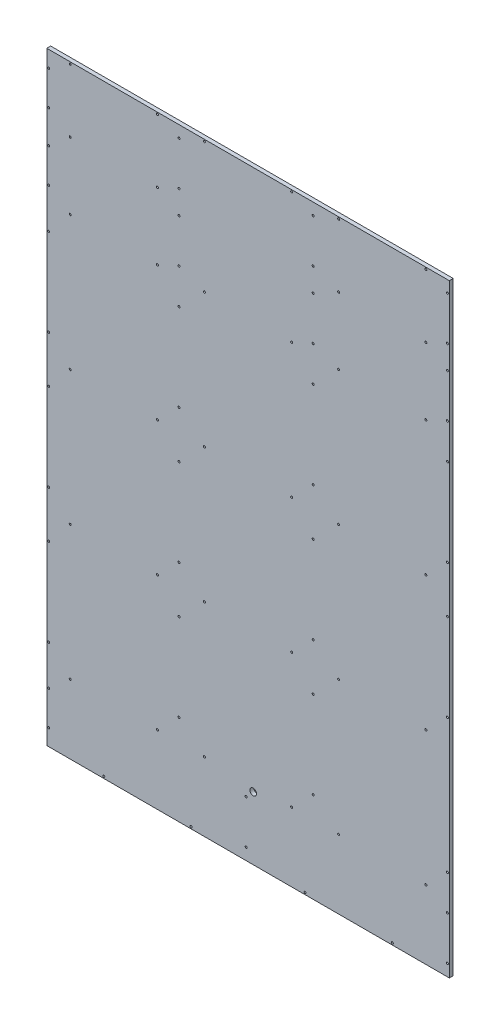
SolidWorks part; units mm, degrees
material "Acrylic (Medium-high impact)"
ref_plane "Front Plane" through (0, 0, 0) normal (0, 0, 1) x (1, 0, 0)
ref_plane "Top Plane" through (0, 0, 0) normal (0, 1, 0) x (1, 0, 0)
ref_plane "Right Plane" through (0, 0, 0) normal (1, 0, 0) x (0, 0, -1)
sketch "Sketch1" plane through (0, 0, 0) normal (0, 0, 1) x (1, 0, 0)
  line L0 (300, 0) -> (300, 100) construction
  line L1 (0, 0) -> (600, 0)
  line L2 (0, 0) -> (0, 900)
  line L3 (0, 900) -> (600, 900)
  line L4 (600, 0) -> (600, 900)
  line L5 (0, 300) -> (200, 300) construction
  line L6 (0, 100) -> (300, 100) construction
  line L7 (0, 500) -> (600, 500) construction
  line L8 (200, 100) -> (200, 300) construction
  line L10 (150, 5.8) -> (150, 0) construction
  line L11 (156.7, 5.8) -> (156.7, 0) construction
  line L12 (100, 105.8) -> (100, 100) construction
  line L13 (0, 700) -> (200, 700) construction
  line L14 (106.7, 705.8) -> (106.7, 700) construction
  line L15 (594.2, 15.8) -> (594.2, 84.2)
  line L16 (200, 700) -> (200, 800) construction
  line L17 (329.2, 5.8) -> (584.2, 5.8)
  line L20 (0, 294.2) -> (200, 294.2) construction
  line L21 (200, 300) -> (200, 294.2) construction
  line L22 (319.2, 84.2) -> (319.2, 15.8)
  line L23 (0, 200) -> (194.2, 200) construction
  line L25 (200, 300) -> (200, 100) construction
  line L26 (200, 100) -> (194.2, 100) construction
  line L27 (194.2, 300) -> (194.2, 100) construction
  line L28 (100, 294.2) -> (100, 105.8) construction
  line L29 (194.2, 115.8) -> (194.2, 284.2)
  line L30 (29.2, 105.8) -> (184.2, 105.8)
  line L31 (19.2, 284.2) -> (19.2, 115.8)
  line L32 (184.2, 294.2) -> (29.2, 294.2)
  line L37 (584.2, 94.2) -> (329.2, 94.2)
  line L43 (600, 0) -> (600, 100) construction
  line L44 (300, 100) -> (600, 100) construction
  line L46 (450, 5.8) -> (450, 0) construction
  line L47 (456.7, 5.8) -> (456.7, 0) construction
  line L48 (394.2, 115.8) -> (394.2, 284.2)
  line L55 (500, 100) -> (494.2, 100) construction
  line L57 (200, 800) -> (0, 800) construction
  line L58 (300, 100) -> (600, 100) construction
  line L59 (600, 100) -> (600, 0) construction
  line L60 (450, 100) -> (450, 5.8) construction
  line L61 (456.7, 94.2) -> (456.7, 100) construction
  line L62 (594.2, 50) -> (600, 50) construction
  line L63 (300, 50) -> (600, 50) construction
  line L64 (600, 100) -> (600, 0) construction
  line L69 (229.2, 105.8) -> (384.2, 105.8)
  line L70 (219.2, 284.2) -> (219.2, 115.8)
  line L71 (384.2, 294.2) -> (229.2, 294.2)
  line L72 (200, 300) -> (400, 300) construction
  line L74 (400, 100) -> (400, 300) construction
  line L75 (300, 105.8) -> (300, 100) construction
  line L76 (200, 294.2) -> (400, 294.2) construction
  line L78 (400, 300) -> (400, 294.2) construction
  line L79 (200, 200) -> (394.2, 200) construction
  line L80 (400, 300) -> (400, 100) construction
  line L85 (394.2, 300) -> (394.2, 100) construction
  line L86 (300, 294.2) -> (300, 105.8) construction
  line L87 (400, 300) -> (394.2, 300) construction
  line L88 (594.2, 115.8) -> (594.2, 284.2)
  line L89 (429.2, 105.8) -> (584.2, 105.8)
  line L90 (419.2, 284.2) -> (419.2, 115.8)
  line L91 (584.2, 294.2) -> (429.2, 294.2)
  line L92 (400, 300) -> (600, 300) construction
  line L93 (600, 100) -> (600, 300) construction
  line L94 (500, 105.8) -> (500, 100) construction
  line L95 (400, 294.2) -> (600, 294.2) construction
  line L96 (600, 300) -> (600, 294.2) construction
  line L101 (400, 200) -> (594.2, 200) construction
  line L102 (600, 300) -> (600, 100) construction
  line L103 (594.2, 300) -> (594.2, 100) construction
  line L104 (500, 294.2) -> (500, 105.8) construction
  line L105 (600, 300) -> (594.2, 300) construction
  line L106 (394.2, 315.8) -> (394.2, 484.2)
  line L107 (229.2, 305.8) -> (384.2, 305.8)
  line L108 (219.2, 484.2) -> (219.2, 315.8)
  line L109 (384.2, 494.2) -> (229.2, 494.2)
  line L110 (200, 500) -> (400, 500) construction
  line L111 (400, 300) -> (400, 500) construction
  line L112 (300, 305.8) -> (300, 300) construction
  line L117 (200, 494.2) -> (400, 494.2) construction
  line L118 (400, 500) -> (400, 494.2) construction
  line L119 (200, 400) -> (394.2, 400) construction
  line L120 (400, 500) -> (400, 300) construction
  line L121 (394.2, 500) -> (394.2, 300) construction
  line L122 (300, 494.2) -> (300, 305.8) construction
  line L123 (400, 500) -> (394.2, 500) construction
  line L124 (594.2, 315.8) -> (594.2, 484.2)
  line L125 (429.2, 305.8) -> (584.2, 305.8)
  line L126 (419.2, 484.2) -> (419.2, 315.8)
  line L127 (584.2, 494.2) -> (429.2, 494.2)
  line L128 (400, 500) -> (600, 500) construction
  line L133 (600, 300) -> (600, 500) construction
  line L134 (500, 305.8) -> (500, 300) construction
  line L135 (400, 494.2) -> (600, 494.2) construction
  line L136 (600, 500) -> (600, 494.2) construction
  line L137 (400, 400) -> (594.2, 400) construction
  line L138 (600, 500) -> (600, 300) construction
  line L139 (594.2, 500) -> (594.2, 300) construction
  line L142 (200, 300) -> (194.2, 300) construction
  line L144 (500, 494.2) -> (500, 305.8) construction
  line L149 (600, 500) -> (594.2, 500) construction
  line L150 (394.2, 515.8) -> (394.2, 684.2)
  line L151 (229.2, 505.8) -> (384.2, 505.8)
  line L152 (219.2, 684.2) -> (219.2, 515.8)
  line L153 (384.2, 694.2) -> (229.2, 694.2)
  line L154 (200, 700) -> (400, 700) construction
  line L155 (400, 500) -> (400, 700) construction
  line L156 (300, 505.8) -> (300, 500) construction
  line L157 (200, 694.2) -> (400, 694.2) construction
  line L158 (400, 700) -> (400, 694.2) construction
  line L159 (200, 600) -> (394.2, 600) construction
  line L160 (400, 700) -> (400, 500) construction
  line L165 (0, 100) -> (300, 100) construction
  line L166 (0, 100) -> (0, 0) construction
  line L171 (300, 100) -> (300, 0) construction
  line L176 (150, 100) -> (150, 5.8) construction
  line L177 (156.7, 94.2) -> (156.7, 100) construction
  line L178 (294.2, 50) -> (300, 50) construction
  line L179 (0, 50) -> (300, 50) construction
  line L180 (394.2, 700) -> (394.2, 500) construction
  line L181 (300, 100) -> (300, 0) construction
  line L182 (300, 0) -> (150, 0) construction
  line L183 (300, 694.2) -> (300, 505.8) construction
  line L184 (294.2, 15.8) -> (294.2, 84.2)
  line L185 (29.2, 5.8) -> (284.2, 5.8)
  line L186 (19.2, 84.2) -> (19.2, 15.8)
  line L187 (284.2, 94.2) -> (29.2, 94.2)
  line L188 (400, 700) -> (394.2, 700) construction
  line L189 (594.2, 515.8) -> (594.2, 684.2)
  line L192 (429.2, 505.8) -> (584.2, 505.8)
  line L193 (419.2, 684.2) -> (419.2, 515.8)
  line L194 (584.2, 694.2) -> (429.2, 694.2)
  line L197 (400, 700) -> (600, 700) construction
  line L203 (600, 500) -> (600, 700) construction
  line L204 (500, 505.8) -> (500, 500) construction
  line L206 (100, 700) -> (100, 800) construction
  line L207 (106.7, 794.2) -> (106.7, 800) construction
  line L208 (194.2, 750) -> (200, 750) construction
  line L209 (0, 750) -> (200, 750) construction
  line L211 (400, 694.2) -> (600, 694.2) construction
  line L212 (194.2, 715.8) -> (194.2, 784.2)
  line L213 (29.2, 705.8) -> (184.2, 705.8)
  line L214 (184.2, 794.2) -> (29.2, 794.2)
  line L215 (19.2, 784.2) -> (19.2, 715.8)
  line L220 (600, 700) -> (600, 694.2) construction
  line L222 (400, 600) -> (594.2, 600) construction
  line L223 (600, 700) -> (600, 500) construction
  line L225 (594.2, 700) -> (594.2, 500) construction
  line L226 (500, 694.2) -> (500, 505.8) construction
  line L228 (600, 700) -> (594.2, 700) construction
  line L230 (194.2, 315.8) -> (194.2, 484.2)
  line L235 (29.2, 305.8) -> (184.2, 305.8)
  line L236 (19.2, 484.2) -> (19.2, 315.8)
  line L237 (184.2, 494.2) -> (29.2, 494.2)
  line L238 (0, 500) -> (200, 500) construction
  line L239 (200, 300) -> (200, 500) construction
  line L240 (100, 305.8) -> (100, 300) construction
  line L241 (0, 494.2) -> (200, 494.2) construction
  line L242 (200, 500) -> (200, 494.2) construction
  line L243 (0, 400) -> (194.2, 400) construction
  line L244 (200, 500) -> (200, 300) construction
  line L245 (194.2, 500) -> (194.2, 300) construction
  line L246 (394.2, 833.4299) -> (394.2, 901.8299) [skipped]
  line L247 (229.2, 823.4299) -> (384.2, 823.4299) [skipped]
  line L248 (384.2, 911.8299) -> (229.2, 911.8299) [skipped]
  line L249 (219.2, 901.8299) -> (219.2, 833.4299) [skipped]
  line L250 (100, 494.2) -> (100, 305.8) construction
  line L251 (200, 500) -> (194.2, 500) construction
  line L252 (194.2, 515.8) -> (194.2, 684.2)
  line L253 (29.2, 505.8) -> (184.2, 505.8)
  line L254 (19.2, 684.2) -> (19.2, 515.8)
  line L255 (300, 817.6299) -> (300, 917.6299) construction
  line L256 (306.7, 911.8299) -> (306.7, 917.6299) construction
  line L257 (394.2, 867.6299) -> (400, 867.6299) construction
  line L258 (200, 867.6299) -> (400, 867.6299) construction
  line L259 (184.2, 694.2) -> (29.2, 694.2)
  line L260 (0, 700) -> (200, 700) construction
  line L265 (200, 500) -> (200, 700) construction
  line L266 (100, 505.8) -> (100, 500) construction
  line L267 (0, 694.2) -> (200, 694.2) construction
  line L268 (200, 700) -> (200, 694.2) construction
  line L269 (0, 600) -> (194.2, 600) construction
  line L270 (200, 700) -> (200, 500) construction
  line L271 (194.2, 700) -> (194.2, 500) construction
  line L272 (100, 694.2) -> (100, 505.8) construction
  line L273 (200, 700) -> (194.2, 700) construction
  line L274 (394.2, 715.8) -> (394.2, 784.2)
  line L275 (229.2, 705.8) -> (384.2, 705.8)
  line L280 (384.2, 794.2) -> (229.2, 794.2)
  line L281 (219.2, 784.2) -> (219.2, 715.8)
  line L282 (306.7, 705.8) -> (306.7, 700) construction
  line L283 (400, 700) -> (400, 800) construction
  line L285 (400, 800) -> (200, 800) construction
  line L286 (300, 700) -> (300, 800) construction
  line L288 (306.7, 794.2) -> (306.7, 800) construction
  line L290 (394.2, 750) -> (400, 750) construction
  line L291 (219.2, 783.65) -> (219.2, 750) [skipped]
  line L292 (394.2, 716.35) -> (394.2, 750) [skipped]
  line L293 (300, 705.8) -> (383.65, 705.8) [skipped]
  line L294 (200, 750) -> (300, 750) construction
  line L295 (300, 793.65) -> (300, 800) construction
  line L296 (306.7, 794.2) -> (306.7, 800) construction
  line L297 (306.15, 794.2) -> (300, 794.2) [skipped]
  line L298 (106.7, 911.8299) -> (106.7, 917.6299) construction
  line L299 (106.1501, 911.8299) -> (28.6501, 911.8299) [skipped]
  line L300 (0, 867.6299) -> (18.65, 867.6299) construction
  line L301 (19.2, 850) -> (19.2, 816.35) [skipped]
  line L302 (100, 823.4299) -> (183.65, 823.4299) [skipped]
  line L303 (100, 800) -> (100, 806.35) construction
  line L304 (194.2, 867.6299) -> (200, 867.6299) construction
  line L305 (194.2, 850) -> (194.2, 883.65) [skipped]
  line L306 (394.2, 750) -> (400, 750) construction
  line L307 (200, 750) -> (400, 750) construction
  line L308 (594.2, 715.8) -> (594.2, 784.2)
  line L309 (429.2, 705.8) -> (584.2, 705.8)
  line L310 (584.2, 794.2) -> (429.2, 794.2)
  line L311 (394.2, 115.8) -> (394.2, 284.2) [skipped]
  line L312 (229.2, 105.8) -> (384.2, 105.8) [skipped]
  line L313 (219.2, 284.2) -> (219.2, 115.8) [skipped]
  line L314 (384.2, 294.2) -> (229.2, 294.2) [skipped]
  line L315 (300, 294.2) -> (300, 105.8) construction
  line L316 (200, 200) -> (394.2, 200) construction
  line L317 (394.2, 315.8) -> (394.2, 484.2) [skipped]
  line L318 (219.2, 484.2) -> (219.2, 315.8) [skipped]
  line L319 (384.2, 494.2) -> (229.2, 494.2) [skipped]
  line L320 (200, 494.2) -> (400, 494.2) construction
  line L321 (419.2, 784.2) -> (419.2, 715.8)
  line L322 (200, 400) -> (394.2, 400) construction
  line L323 (394.2, 513.7835) -> (394.2, 300) construction
  line L324 (300, 494.2) -> (300, 305.8) construction
  line L325 (229.2, 305.8) -> (384.2, 305.8) [skipped]
  line L326 (506.7, 705.8) -> (506.7, 700) construction
  line L327 (400, 300) -> (394.2, 300) construction
  line L328 (394.2, 300) -> (394.2, 294.2) construction
  line L329 (400, 100) -> (394.2, 100) construction
  line L330 (400, 294.2) -> (400, 300) construction
  line L331 (600, 700) -> (600, 800) construction
  line L332 (201.4757, 294.2) -> (300.7378, 294.2) construction
  line L333 (400, 313.7835) -> (400, 293.1) construction
  line L334 (600, 800) -> (400, 800) construction
  line L335 (400, 300) -> (400, 294.2) construction
  line L336 (194.2, 315.8) -> (194.2, 484.2) [skipped]
  line L337 (29.2, 305.8) -> (184.2, 305.8) [skipped]
  line L338 (19.2, 484.2) -> (19.2, 315.8) [skipped]
  line L339 (184.2, 494.2) -> (29.2, 494.2) [skipped]
  line L340 (400, 494.2) -> (400, 500) construction
  line L341 (500, 700) -> (500, 800) construction
  line L342 (506.7, 794.2) -> (506.7, 800) construction
  line L343 (400, 513.7835) -> (400, 493.1) construction
  line L344 (594.2, 750) -> (600, 750) construction
  line L345 (400, 500) -> (400, 494.2) construction
  line L346 (200, 300) -> (200, 500) construction
  line L347 (400, 750) -> (600, 750) construction
  line L348 (0, 494.2) -> (200, 494.2) construction
  line L349 (200, 513.7835) -> (200, 493.1) construction
  line L350 (394.2, 815.8) -> (394.2, 884.2) [skipped]
  line L351 (0, 400) -> (194.2, 400) construction
  line L352 (229.2, 805.8) -> (384.2, 805.8) [skipped]
  line L353 (200, 513.7835) -> (200, 300) construction
  line L354 (194.2, 513.7835) -> (194.2, 300) construction
  line L355 (100, 494.2) -> (100, 305.8) construction
  line L356 (384.2, 894.2) -> (229.2, 894.2) [skipped]
  line L357 (219.2, 884.2) -> (219.2, 815.8) [skipped]
  line L358 (306.7, 805.8) -> (306.7, 800) construction
  line L359 (400, 800) -> (400, 900) construction
  line L360 (500, 300) -> (500, 100) construction
  line L361 (400, 900) -> (200, 900) construction
  line L362 (300, 800) -> (300, 900) construction
  line L363 (306.7, 894.2) -> (306.7, 900) construction
  line L364 (394.2, 850) -> (400, 850) construction
  line L365 (200, 850) -> (400, 850) construction
  line L366 (594.2, 815.8) -> (594.2, 884.2)
  line L367 (429.2, 805.8) -> (584.2, 805.8)
  line L368 (584.2, 894.2) -> (429.2, 894.2)
  line L369 (419.2, 884.2) -> (419.2, 815.8)
  line L370 (506.7, 805.8) -> (506.7, 800) construction
  line L371 (600, 800) -> (600, 900) construction
  line L372 (600, 900) -> (400, 900) construction
  line L373 (500, 800) -> (500, 900) construction
  line L374 (506.7, 894.2) -> (506.7, 900) construction
  line L375 (594.2, 850) -> (600, 850) construction
  line L376 (400, 850) -> (600, 850) construction
  line L377 (194.2, 815.8) -> (194.2, 884.2)
  line L378 (29.2, 805.8) -> (184.2, 805.8)
  line L379 (184.2, 894.2) -> (29.2, 894.2)
  line L380 (19.2, 884.2) -> (19.2, 815.8)
  line L381 (106.7, 805.8) -> (106.7, 800) construction
  line L382 (200, 800) -> (200, 900) construction
  line L383 (200, 900) -> (0, 900) construction
  line L384 (100, 800) -> (100, 900) construction
  line L385 (106.7, 894.2) -> (106.7, 900) construction
  line L386 (194.2, 850) -> (200, 850) construction
  line L387 (0, 850) -> (200, 850) construction
  circle A2 centre (165, 102.9) radius 1.5
  circle A3 centre (35, 102.9) radius 1.5
  circle A4 centre (197.1, 265) radius 1.5
  circle A5 centre (197.1, 135) radius 1.5
  circle A6 centre (2.9, 135) radius 1.5
  circle A7 centre (2.9, 265) radius 1.5
  circle A8 centre (10.9, 265) radius 1.5
  circle A9 centre (10.9, 135) radius 1.5
  arc A10 (184.2, 105.8) -> (194.2, 115.8) centre (184.2, 115.8) ccw
  arc A11 (19.2, 115.8) -> (29.2, 105.8) centre (29.2, 115.8) ccw
  arc A12 (29.2, 294.2) -> (19.2, 284.2) centre (29.2, 284.2) ccw
  arc A13 (194.2, 284.2) -> (184.2, 294.2) centre (184.2, 284.2) ccw
  circle A140 centre (85, 2.9) radius 1.5
  circle A141 centre (215, 2.9) radius 1.5
  circle A144 centre (297.1, 82.5) radius 1.5
  circle A145 centre (297.1, 17.5) radius 1.5
  circle A146 centre (2.9, 24.5) radius 1.5
  circle A147 centre (2.9, 75.5) radius 1.5
  circle A148 centre (10.9, 75.5) radius 1.5
  circle A149 centre (10.9, 24.5) radius 1.5
  arc A150 (284.2, 5.8) -> (294.2, 15.8) centre (284.2, 15.8) ccw
  arc A151 (19.2, 15.8) -> (29.2, 5.8) centre (29.2, 15.8) ccw
  arc A152 (29.2, 94.2) -> (19.2, 84.2) centre (29.2, 84.2) ccw
  arc A153 (294.2, 84.2) -> (284.2, 94.2) centre (284.2, 84.2) ccw
  circle A168 centre (35, 702.9) radius 1.5
  circle A169 centre (165, 702.9) radius 1.5
  circle A172 centre (197.1, 782.5) radius 1.5
  circle A173 centre (197.1, 717.5) radius 1.5
  circle A174 centre (2.9, 775.5) radius 1.5
  circle A175 centre (10.9, 775.5) radius 1.5
  circle A176 centre (2.9, 724.5) radius 1.5
  circle A177 centre (10.9, 724.5) radius 1.5
  arc A178 (19.2, 715.8) -> (29.2, 705.8) centre (29.2, 715.8) ccw
  arc A179 (184.2, 705.8) -> (194.2, 715.8) centre (184.2, 715.8) ccw
  arc A180 (194.2, 784.2) -> (184.2, 794.2) centre (184.2, 784.2) ccw
  arc A181 (29.2, 794.2) -> (19.2, 784.2) centre (29.2, 784.2) ccw
  circle A210 centre (235, 820.5299) radius 1.5 [skipped]
  circle A211 centre (365, 820.5299) radius 1.5 [skipped]
  circle A214 centre (397.1, 900.1299) radius 1.5 [skipped]
  circle A215 centre (397.1, 835.1299) radius 1.5 [skipped]
  circle A216 centre (202.9, 893.1299) radius 1.5 [skipped]
  circle A217 centre (210.9, 893.1299) radius 1.5 [skipped]
  circle A218 centre (202.9, 842.1299) radius 1.5 [skipped]
  circle A219 centre (210.9, 842.1299) radius 1.5 [skipped]
  arc A220 (219.2, 833.4299) -> (229.2, 823.4299) centre (229.2, 833.4299) ccw [skipped]
  arc A221 (384.2, 823.4299) -> (394.2, 833.4299) centre (384.2, 833.4299) ccw [skipped]
  arc A222 (394.2, 901.8299) -> (384.2, 911.8299) centre (384.2, 901.8299) ccw [skipped]
  arc A223 (229.2, 911.8299) -> (219.2, 901.8299) centre (229.2, 901.8299) ccw [skipped]
  circle A252 centre (385, 2.9) radius 1.5
  circle A253 centre (515, 2.9) radius 1.5
  circle A254 centre (597.1, 82.5) radius 1.5
  circle A255 centre (597.1, 17.5) radius 1.5
  circle A256 centre (302.9, 24.5) radius 1.5
  circle A257 centre (302.9, 75.5) radius 1.5
  circle A258 centre (310.9, 75.5) radius 1.5
  circle A259 centre (310.9, 24.5) radius 1.5
  arc A260 (584.2, 5.8) -> (594.2, 15.8) centre (584.2, 15.8) ccw
  arc A261 (319.2, 15.8) -> (329.2, 5.8) centre (329.2, 15.8) ccw
  arc A262 (329.2, 94.2) -> (319.2, 84.2) centre (329.2, 84.2) ccw
  arc A263 (594.2, 84.2) -> (584.2, 94.2) centre (584.2, 84.2) ccw
  circle A264 centre (365, 102.9) radius 1.5
  circle A265 centre (235, 102.9) radius 1.5
  circle A266 centre (397.1, 265) radius 1.5
  circle A267 centre (397.1, 135) radius 1.5
  circle A268 centre (202.9, 135) radius 1.5
  circle A269 centre (202.9, 265) radius 1.5
  arc A272 (219.2, 715.8) -> (229.2, 705.8) centre (229.2, 715.8) ccw [skipped]
  circle A273 centre (235, 702.9) radius 1.5 [skipped]
  circle A274 centre (210.9, 724.5) radius 1.5 [skipped]
  circle A275 centre (202.9, 724.5) radius 1.5 [skipped]
  circle A276 centre (210.9, 775.5) radius 1.5 [skipped]
  circle A277 centre (202.9, 775.5) radius 1.5 [skipped]
  arc A278 (229.2, 794.2) -> (219.2, 784.2) centre (229.2, 784.2) ccw [skipped]
  arc A279 (394.2, 784.2) -> (384.2, 794.2) centre (384.2, 784.2) ccw [skipped]
  circle A280 centre (397.1, 782.5) radius 1.5 [skipped]
  arc A281 (384.2, 705.8) -> (394.2, 715.8) centre (384.2, 715.8) ccw [skipped]
  circle A282 centre (397.1, 717.5) radius 1.5 [skipped]
  circle A283 centre (365, 702.9) radius 1.5 [skipped]
  arc A284 (29.2, 911.8299) -> (19.2, 901.8299) centre (29.2, 901.8299) ccw [skipped]
  circle A285 centre (10.9, 893.1299) radius 1.5 [skipped]
  circle A286 centre (2.9, 893.1299) radius 1.5 [skipped]
  circle A287 centre (10.9, 842.1299) radius 1.5 [skipped]
  circle A288 centre (2.9, 842.1299) radius 1.5 [skipped]
  arc A289 (19.2, 833.4299) -> (29.2, 823.4299) centre (29.2, 833.4299) ccw [skipped]
  circle A290 centre (35, 820.5299) radius 1.5 [skipped]
  circle A291 centre (165, 820.5299) radius 1.5 [skipped]
  arc A292 (184.2, 823.4299) -> (194.2, 833.4299) centre (184.2, 833.4299) ccw [skipped]
  circle A293 centre (197.1, 835.1299) radius 1.5 [skipped]
  circle A294 centre (197.1, 900.1299) radius 1.5 [skipped]
  arc A295 (194.2, 901.8299) -> (184.2, 911.8299) centre (184.2, 901.8299) ccw [skipped]
  circle A296 centre (210.9, 265) radius 1.5 [skipped]
  circle A297 centre (210.9, 135) radius 1.5 [skipped]
  arc A298 (384.2, 105.8) -> (394.2, 115.8) centre (384.2, 115.8) ccw [skipped]
  arc A299 (219.2, 115.8) -> (229.2, 105.8) centre (229.2, 115.8) ccw [skipped]
  arc A300 (229.2, 294.2) -> (219.2, 284.2) centre (229.2, 284.2) ccw [skipped]
  arc A301 (394.2, 284.2) -> (384.2, 294.2) centre (384.2, 284.2) ccw [skipped]
  circle A302 centre (202.9, 135) radius 1.5 [skipped]
  circle A303 centre (202.9, 265) radius 1.5 [skipped]
  circle A304 centre (397.1, 465) radius 1.5 [skipped]
  circle A305 centre (397.1, 335) radius 1.5 [skipped]
  circle A306 centre (202.9, 335) radius 1.5 [skipped]
  circle A307 centre (202.9, 465) radius 1.5 [skipped]
  circle A308 centre (210.9, 465) radius 1.5 [skipped]
  circle A309 centre (210.9, 335) radius 1.5 [skipped]
  arc A310 (384.2, 305.8) -> (394.2, 315.8) centre (384.2, 315.8) ccw [skipped]
  arc A311 (219.2, 315.8) -> (229.2, 305.8) centre (229.2, 315.8) ccw [skipped]
  arc A312 (229.2, 494.2) -> (219.2, 484.2) centre (229.2, 484.2) ccw [skipped]
  arc A313 (394.2, 484.2) -> (384.2, 494.2) centre (384.2, 484.2) ccw [skipped]
  circle A314 centre (397.1, 265) radius 1.5 [skipped]
  circle A315 centre (365, 102.9) radius 1.5 [skipped]
  circle A316 centre (397.1, 135) radius 1.5 [skipped]
  circle A317 centre (365, 302.9) radius 1.5 [skipped]
  circle A318 centre (235, 302.9) radius 1.5 [skipped]
  circle A319 centre (165, 302.9) radius 1.5 [skipped]
  circle A320 centre (35, 302.9) radius 1.5 [skipped]
  circle A321 centre (197.1, 465) radius 1.5 [skipped]
  circle A322 centre (197.1, 335) radius 1.5 [skipped]
  circle A323 centre (10.9, 465) radius 1.5 [skipped]
  circle A324 centre (10.9, 335) radius 1.5 [skipped]
  arc A325 (184.2, 305.8) -> (194.2, 315.8) centre (184.2, 315.8) ccw [skipped]
  arc A326 (19.2, 315.8) -> (29.2, 305.8) centre (29.2, 315.8) ccw [skipped]
  arc A327 (29.2, 494.2) -> (19.2, 484.2) centre (29.2, 484.2) ccw [skipped]
  arc A328 (194.2, 484.2) -> (184.2, 494.2) centre (184.2, 484.2) ccw [skipped]
  circle A329 centre (2.9, 335) radius 1.5 [skipped]
  circle A330 centre (2.9, 465) radius 1.5 [skipped]
  circle A331 centre (235, 102.9) radius 1.5 [skipped]
  circle A332 centre (210.9, 265) radius 1.5
  circle A333 centre (210.9, 135) radius 1.5
  arc A334 (384.2, 105.8) -> (394.2, 115.8) centre (384.2, 115.8) ccw
  arc A335 (219.2, 115.8) -> (229.2, 105.8) centre (229.2, 115.8) ccw
  arc A336 (229.2, 294.2) -> (219.2, 284.2) centre (229.2, 284.2) ccw
  arc A337 (394.2, 284.2) -> (384.2, 294.2) centre (384.2, 284.2) ccw
  circle A338 centre (565, 102.9) radius 1.5
  circle A339 centre (435, 102.9) radius 1.5
  circle A340 centre (597.1, 265) radius 1.5
  circle A341 centre (597.1, 135) radius 1.5
  circle A342 centre (402.9, 135) radius 1.5
  circle A343 centre (402.9, 265) radius 1.5
  circle A344 centre (410.9, 265) radius 1.5
  circle A345 centre (410.9, 135) radius 1.5
  arc A346 (584.2, 105.8) -> (594.2, 115.8) centre (584.2, 115.8) ccw
  arc A347 (419.2, 115.8) -> (429.2, 105.8) centre (429.2, 115.8) ccw
  arc A348 (429.2, 294.2) -> (419.2, 284.2) centre (429.2, 284.2) ccw
  arc A349 (594.2, 284.2) -> (584.2, 294.2) centre (584.2, 284.2) ccw
  circle A350 centre (365, 302.9) radius 1.5
  circle A351 centre (235, 302.9) radius 1.5
  circle A352 centre (397.1, 465) radius 1.5
  circle A353 centre (397.1, 335) radius 1.5
  circle A354 centre (202.9, 335) radius 1.5
  circle A355 centre (202.9, 465) radius 1.5
  circle A356 centre (210.9, 465) radius 1.5
  circle A357 centre (210.9, 335) radius 1.5
  arc A358 (384.2, 305.8) -> (394.2, 315.8) centre (384.2, 315.8) ccw
  arc A359 (219.2, 315.8) -> (229.2, 305.8) centre (229.2, 315.8) ccw
  arc A360 (229.2, 494.2) -> (219.2, 484.2) centre (229.2, 484.2) ccw
  arc A361 (394.2, 484.2) -> (384.2, 494.2) centre (384.2, 484.2) ccw
  circle A362 centre (565, 302.9) radius 1.5
  circle A363 centre (435, 302.9) radius 1.5
  circle A364 centre (597.1, 465) radius 1.5
  circle A365 centre (597.1, 335) radius 1.5
  circle A366 centre (402.9, 335) radius 1.5
  circle A367 centre (402.9, 465) radius 1.5
  circle A368 centre (410.9, 465) radius 1.5
  circle A369 centre (410.9, 335) radius 1.5
  arc A370 (584.2, 305.8) -> (594.2, 315.8) centre (584.2, 315.8) ccw
  arc A371 (419.2, 315.8) -> (429.2, 305.8) centre (429.2, 315.8) ccw
  arc A372 (429.2, 494.2) -> (419.2, 484.2) centre (429.2, 484.2) ccw
  arc A373 (594.2, 484.2) -> (584.2, 494.2) centre (584.2, 484.2) ccw
  circle A374 centre (365, 502.9) radius 1.5
  circle A375 centre (235, 502.9) radius 1.5
  circle A376 centre (397.1, 665) radius 1.5
  circle A377 centre (397.1, 535) radius 1.5
  circle A378 centre (202.9, 535) radius 1.5
  circle A379 centre (202.9, 665) radius 1.5
  circle A380 centre (210.9, 665) radius 1.5
  circle A381 centre (210.9, 535) radius 1.5
  arc A382 (384.2, 505.8) -> (394.2, 515.8) centre (384.2, 515.8) ccw
  arc A383 (219.2, 515.8) -> (229.2, 505.8) centre (229.2, 515.8) ccw
  arc A384 (229.2, 694.2) -> (219.2, 684.2) centre (229.2, 684.2) ccw
  arc A385 (394.2, 684.2) -> (384.2, 694.2) centre (384.2, 684.2) ccw
  circle A386 centre (565, 502.9) radius 1.5
  circle A387 centre (435, 502.9) radius 1.5
  circle A388 centre (597.1, 665) radius 1.5
  circle A389 centre (597.1, 535) radius 1.5
  circle A390 centre (402.9, 535) radius 1.5
  circle A391 centre (402.9, 665) radius 1.5
  circle A392 centre (410.9, 665) radius 1.5
  circle A393 centre (410.9, 535) radius 1.5
  arc A394 (584.2, 505.8) -> (594.2, 515.8) centre (584.2, 515.8) ccw
  arc A395 (419.2, 515.8) -> (429.2, 505.8) centre (429.2, 515.8) ccw
  arc A396 (429.2, 694.2) -> (419.2, 684.2) centre (429.2, 684.2) ccw
  arc A397 (594.2, 684.2) -> (584.2, 694.2) centre (584.2, 684.2) ccw
  circle A398 centre (165, 302.9) radius 1.5
  circle A399 centre (35, 302.9) radius 1.5
  circle A400 centre (197.1, 465) radius 1.5
  circle A401 centre (197.1, 335) radius 1.5
  circle A402 centre (2.9, 335) radius 1.5
  circle A403 centre (2.9, 465) radius 1.5
  circle A404 centre (10.9, 465) radius 1.5
  circle A405 centre (10.9, 335) radius 1.5
  arc A406 (184.2, 305.8) -> (194.2, 315.8) centre (184.2, 315.8) ccw
  arc A407 (19.2, 315.8) -> (29.2, 305.8) centre (29.2, 315.8) ccw
  arc A408 (29.2, 494.2) -> (19.2, 484.2) centre (29.2, 484.2) ccw
  arc A409 (194.2, 484.2) -> (184.2, 494.2) centre (184.2, 484.2) ccw
  circle A410 centre (165, 502.9) radius 1.5
  circle A411 centre (35, 502.9) radius 1.5
  circle A412 centre (197.1, 665) radius 1.5
  circle A413 centre (197.1, 535) radius 1.5
  circle A414 centre (2.9, 535) radius 1.5
  circle A415 centre (2.9, 665) radius 1.5
  circle A416 centre (10.9, 665) radius 1.5
  circle A417 centre (10.9, 535) radius 1.5
  arc A418 (184.2, 505.8) -> (194.2, 515.8) centre (184.2, 515.8) ccw
  arc A419 (19.2, 515.8) -> (29.2, 505.8) centre (29.2, 515.8) ccw
  arc A420 (29.2, 694.2) -> (19.2, 684.2) centre (29.2, 684.2) ccw
  arc A421 (194.2, 684.2) -> (184.2, 694.2) centre (184.2, 684.2) ccw
  circle A422 centre (235, 702.9) radius 1.5
  circle A423 centre (365, 702.9) radius 1.5
  circle A424 centre (397.1, 782.5) radius 1.5
  circle A425 centre (397.1, 717.5) radius 1.5
  circle A426 centre (202.9, 775.5) radius 1.5
  circle A427 centre (210.9, 775.5) radius 1.5
  circle A428 centre (202.9, 724.5) radius 1.5
  circle A429 centre (210.9, 724.5) radius 1.5
  arc A430 (219.2, 715.8) -> (229.2, 705.8) centre (229.2, 715.8) ccw
  arc A431 (384.2, 705.8) -> (394.2, 715.8) centre (384.2, 715.8) ccw
  arc A432 (394.2, 784.2) -> (384.2, 794.2) centre (384.2, 784.2) ccw
  arc A433 (229.2, 794.2) -> (219.2, 784.2) centre (229.2, 784.2) ccw
  circle A434 centre (435, 702.9) radius 1.5
  circle A435 centre (565, 702.9) radius 1.5
  circle A436 centre (597.1, 782.5) radius 1.5
  circle A437 centre (597.1, 717.5) radius 1.5
  circle A438 centre (402.9, 775.5) radius 1.5
  circle A439 centre (410.9, 775.5) radius 1.5
  circle A440 centre (402.9, 724.5) radius 1.5
  circle A441 centre (410.9, 724.5) radius 1.5
  arc A442 (419.2, 715.8) -> (429.2, 705.8) centre (429.2, 715.8) ccw
  arc A443 (584.2, 705.8) -> (594.2, 715.8) centre (584.2, 715.8) ccw
  arc A444 (594.2, 784.2) -> (584.2, 794.2) centre (584.2, 784.2) ccw
  arc A445 (429.2, 794.2) -> (419.2, 784.2) centre (429.2, 784.2) ccw
  circle A446 centre (235, 802.9) radius 1.5 [skipped]
  circle A447 centre (365, 802.9) radius 1.5 [skipped]
  circle A448 centre (397.1, 882.5) radius 1.5 [skipped]
  circle A449 centre (397.1, 817.5) radius 1.5 [skipped]
  circle A450 centre (202.9, 875.5) radius 1.5 [skipped]
  circle A451 centre (210.9, 875.5) radius 1.5 [skipped]
  circle A452 centre (202.9, 824.5) radius 1.5 [skipped]
  circle A453 centre (210.9, 824.5) radius 1.5 [skipped]
  arc A454 (219.2, 815.8) -> (229.2, 805.8) centre (229.2, 815.8) ccw [skipped]
  arc A455 (384.2, 805.8) -> (394.2, 815.8) centre (384.2, 815.8) ccw [skipped]
  arc A456 (394.2, 884.2) -> (384.2, 894.2) centre (384.2, 884.2) ccw [skipped]
  arc A457 (229.2, 894.2) -> (219.2, 884.2) centre (229.2, 884.2) ccw [skipped]
  circle A458 centre (435, 802.9) radius 1.5
  circle A459 centre (565, 802.9) radius 1.5
  circle A460 centre (597.1, 882.5) radius 1.5
  circle A461 centre (597.1, 817.5) radius 1.5
  circle A462 centre (402.9, 875.5) radius 1.5
  circle A463 centre (410.9, 875.5) radius 1.5
  circle A464 centre (402.9, 824.5) radius 1.5
  circle A465 centre (410.9, 824.5) radius 1.5
  arc A466 (419.2, 815.8) -> (429.2, 805.8) centre (429.2, 815.8) ccw
  arc A467 (584.2, 805.8) -> (594.2, 815.8) centre (584.2, 815.8) ccw
  arc A468 (594.2, 884.2) -> (584.2, 894.2) centre (584.2, 884.2) ccw
  arc A469 (429.2, 894.2) -> (419.2, 884.2) centre (429.2, 884.2) ccw
  circle A470 centre (35, 802.9) radius 1.5
  circle A471 centre (165, 802.9) radius 1.5
  circle A472 centre (197.1, 882.5) radius 1.5
  circle A473 centre (197.1, 817.5) radius 1.5
  circle A474 centre (2.9, 875.5) radius 1.5
  circle A475 centre (10.9, 875.5) radius 1.5
  circle A476 centre (2.9, 824.5) radius 1.5
  circle A477 centre (10.9, 824.5) radius 1.5
  arc A478 (19.2, 815.8) -> (29.2, 805.8) centre (29.2, 815.8) ccw
  arc A479 (184.2, 805.8) -> (194.2, 815.8) centre (184.2, 815.8) ccw
  arc A480 (194.2, 884.2) -> (184.2, 894.2) centre (184.2, 884.2) ccw
  arc A481 (29.2, 894.2) -> (19.2, 884.2) centre (29.2, 884.2) ccw
  circle A482 centre (397.1, 817.5) radius 1.5
  circle A483 centre (397.1, 882.5) radius 1.5
  circle A484 centre (165, 897.1) radius 1.5
  circle A485 centre (35, 897.1) radius 1.5
  circle A486 centre (235, 897.1) radius 1.5
  circle A487 centre (365, 897.1) radius 1.5
  circle A488 centre (435, 897.1) radius 1.5
  circle A489 centre (565, 897.1) radius 1.5
  point P9 (150, 2.9)
  point P14 (100, 102.9)
  point P15 (156.7, 2.9)
  point P16 (100, 750)
  point P19 (106.7, 702.9)
  point P487 (297.1, 50)
  point P578 (197.1, 750)
  dimension "D24" = 5.8
  dimension "D16" = 3
  dimension "D25" = 10
  dimension "D26" = 10
  dimension "D30" = 10
  dimension "D41" = 10
  dimension "D42" = 10
  dimension "D43" = 10
  dimension "D1" = 600
  dimension "D2" = 900
  dimension "D3" = 200
  dimension "D4" = 200
  dimension "D5" = 100
  dimension "D6" = 200
  dimension "D7" = 130
  dimension "D8" = 65
  dimension "D9" = 175
  dimension "D10" = 2
  dimension "D11" = 2
  dimension "D12" = 2
  dimension "D13" = 2
  dimension "D14" = 5.8
  dimension "D15" = 25.5
  dimension "D17" = 25.5
  dimension "D18" = 32.5
  dimension "D19" = 2.9
  dimension "D20" = 5.8
  dimension "D21" = 8
  dimension "D22" = 275
  dimension "D23" = 5.8
  dimension "D27" = 8
  dimension "D28" = 5.8
  dimension "D29" = 5.8
  dimension "D31" = 65
  dimension "D32" = 65
  dimension "D33" = 100
  dimension "D34" = 175
  dimension "D35" = 200
  dimension "D36" = 100
  dimension "D37" = 8
  dimension "D38" = 5.8
  dimension "D39" = 5.8
  dimension "D40" = 5.8
  dimension "D44" = 32.5
  dimension "D50" = 100
  dimension "D45" = 2
  dimension "D48" = 3
  dimension "D49" = 3
  dimension "D46" = 3
  dimension "D47" = 2
extrude "Boss-Extrude1" add sketch "Sketch1" along normal blind 5.8
sketch "Sketch2" plane through (0, 0, 5.8) normal (0, 0, -1) x (-1, 0, 0)
  line L13 (-29.2, 894.2) -> (-184.2, 894.2)
  line L38 (-194.2, 884.2) -> (-194.2, 815.8)
  line L43 (-184.2, 805.8) -> (-29.2, 805.8)
  line L44 (-19.2, 815.8) -> (-19.2, 884.2)
  line L49 (-29.2, 894.2) -> (-184.2, 894.2)
  line L50 (-194.2, 884.2) -> (-194.2, 815.8)
  line L87 (-184.2, 805.8) -> (-29.2, 805.8)
  line L88 (-19.2, 815.8) -> (-19.2, 884.2)
  line L99 (-429.2, 894.2) -> (-584.2, 894.2)
  line L100 (-594.2, 884.2) -> (-594.2, 815.8)
  line L105 (-584.2, 805.8) -> (-429.2, 805.8)
  line L106 (-419.2, 815.8) -> (-419.2, 884.2)
  line L111 (-429.2, 894.2) -> (-584.2, 894.2)
  line L112 (-594.2, 884.2) -> (-594.2, 815.8)
  line L117 (-584.2, 805.8) -> (-429.2, 805.8)
  line L118 (-419.2, 815.8) -> (-419.2, 884.2)
  line L123 (-429.2, 794.2) -> (-584.2, 794.2)
  line L124 (-594.2, 784.2) -> (-594.2, 715.8)
  line L130 (-584.2, 705.8) -> (-429.2, 705.8)
  line L135 (-419.2, 715.8) -> (-419.2, 784.2)
  line L136 (-429.2, 794.2) -> (-584.2, 794.2)
  line L141 (-594.2, 784.2) -> (-594.2, 715.8)
  line L142 (-584.2, 705.8) -> (-429.2, 705.8)
  line L143 (-419.2, 715.8) -> (-419.2, 784.2)
  line L144 (-229.2, 794.2) -> (-384.2, 794.2)
  line L145 (-394.2, 784.2) -> (-394.2, 715.8)
  line L146 (-384.2, 705.8) -> (-229.2, 705.8)
  line L147 (-219.2, 715.8) -> (-219.2, 784.2)
  line L149 (-229.2, 794.2) -> (-384.2, 794.2)
  line L150 (-394.2, 784.2) -> (-394.2, 715.8)
  line L155 (-384.2, 705.8) -> (-229.2, 705.8)
  line L156 (-219.2, 715.8) -> (-219.2, 784.2)
  line L161 (-194.2, 684.2) -> (-194.2, 515.8)
  line L162 (-184.2, 505.8) -> (-29.2, 505.8)
  line L166 (-19.2, 515.8) -> (-19.2, 684.2)
  line L167 (-29.2, 694.2) -> (-184.2, 694.2)
  line L169 (-194.2, 684.2) -> (-194.2, 515.8)
  line L170 (-184.2, 505.8) -> (-29.2, 505.8)
  line L171 (-19.2, 515.8) -> (-19.2, 684.2)
  line L172 (-29.2, 694.2) -> (-184.2, 694.2)
  line L173 (-194.2, 484.2) -> (-194.2, 315.8)
  line L174 (-184.2, 305.8) -> (-29.2, 305.8)
  line L175 (-19.2, 315.8) -> (-19.2, 484.2)
  line L176 (-29.2, 494.2) -> (-184.2, 494.2)
  line L177 (-194.2, 484.2) -> (-194.2, 315.8)
  line L178 (-184.2, 305.8) -> (-29.2, 305.8)
  line L179 (-19.2, 315.8) -> (-19.2, 484.2)
  line L180 (-29.2, 494.2) -> (-184.2, 494.2)
  line L181 (-594.2, 684.2) -> (-594.2, 515.8)
  line L182 (-584.2, 505.8) -> (-429.2, 505.8)
  line L183 (-419.2, 515.8) -> (-419.2, 684.2)
  line L184 (-429.2, 694.2) -> (-584.2, 694.2)
  line L185 (-594.2, 684.2) -> (-594.2, 515.8)
  line L186 (-584.2, 505.8) -> (-429.2, 505.8)
  line L187 (-419.2, 515.8) -> (-419.2, 684.2)
  line L188 (-429.2, 694.2) -> (-584.2, 694.2)
  line L189 (-394.2, 684.2) -> (-394.2, 515.8)
  line L190 (-384.2, 505.8) -> (-229.2, 505.8)
  line L191 (-219.2, 515.8) -> (-219.2, 684.2)
  line L192 (-229.2, 694.2) -> (-384.2, 694.2)
  line L193 (-394.2, 684.2) -> (-394.2, 515.8)
  line L194 (-384.2, 505.8) -> (-229.2, 505.8)
  line L195 (-219.2, 515.8) -> (-219.2, 684.2)
  line L196 (-229.2, 694.2) -> (-384.2, 694.2)
  line L197 (-594.2, 484.2) -> (-594.2, 315.8)
  line L198 (-584.2, 305.8) -> (-429.2, 305.8)
  line L199 (-419.2, 315.8) -> (-419.2, 484.2)
  line L200 (-429.2, 494.2) -> (-584.2, 494.2)
  line L201 (-594.2, 484.2) -> (-594.2, 315.8)
  line L202 (-584.2, 305.8) -> (-429.2, 305.8)
  line L203 (-419.2, 315.8) -> (-419.2, 484.2)
  line L204 (-429.2, 494.2) -> (-584.2, 494.2)
  line L205 (-394.2, 484.2) -> (-394.2, 315.8)
  line L206 (-384.2, 305.8) -> (-229.2, 305.8)
  line L207 (-219.2, 315.8) -> (-219.2, 484.2)
  line L208 (-229.2, 494.2) -> (-384.2, 494.2)
  line L209 (-394.2, 484.2) -> (-394.2, 315.8)
  line L210 (-384.2, 305.8) -> (-229.2, 305.8)
  line L211 (-219.2, 315.8) -> (-219.2, 484.2)
  line L212 (-229.2, 494.2) -> (-384.2, 494.2)
  line L213 (-594.2, 284.2) -> (-594.2, 115.8)
  line L214 (-584.2, 105.8) -> (-429.2, 105.8)
  line L215 (-419.2, 115.8) -> (-419.2, 284.2)
  line L216 (-429.2, 294.2) -> (-584.2, 294.2)
  line L217 (-594.2, 284.2) -> (-594.2, 115.8)
  line L218 (-584.2, 105.8) -> (-429.2, 105.8)
  line L219 (-419.2, 115.8) -> (-419.2, 284.2)
  line L220 (-429.2, 294.2) -> (-584.2, 294.2)
  line L221 (-394.2, 284.2) -> (-394.2, 115.8)
  line L222 (-384.2, 105.8) -> (-229.2, 105.8)
  line L223 (-219.2, 115.8) -> (-219.2, 284.2)
  line L224 (-229.2, 294.2) -> (-384.2, 294.2)
  line L225 (-394.2, 284.2) -> (-394.2, 115.8)
  line L226 (-384.2, 105.8) -> (-229.2, 105.8)
  line L227 (-219.2, 115.8) -> (-219.2, 284.2)
  line L228 (-229.2, 294.2) -> (-384.2, 294.2)
  line L229 (-594.2, 84.2) -> (-594.2, 15.8)
  line L230 (-584.2, 5.8) -> (-329.2, 5.8)
  line L231 (-319.2, 15.8) -> (-319.2, 84.2)
  line L232 (-329.2, 94.2) -> (-584.2, 94.2)
  line L233 (-594.2, 84.2) -> (-594.2, 15.8)
  line L234 (-584.2, 5.8) -> (-329.2, 5.8)
  line L235 (-319.2, 15.8) -> (-319.2, 84.2)
  line L236 (-329.2, 94.2) -> (-584.2, 94.2)
  line L237 (-29.2, 794.2) -> (-184.2, 794.2)
  line L238 (-194.2, 784.2) -> (-194.2, 715.8)
  line L239 (-184.2, 705.8) -> (-29.2, 705.8)
  line L240 (-19.2, 715.8) -> (-19.2, 784.2)
  line L241 (-29.2, 794.2) -> (-184.2, 794.2)
  line L242 (-194.2, 784.2) -> (-194.2, 715.8)
  line L243 (-184.2, 705.8) -> (-29.2, 705.8)
  line L244 (-19.2, 715.8) -> (-19.2, 784.2)
  line L245 (-294.2, 84.2) -> (-294.2, 15.8)
  line L246 (-284.2, 5.8) -> (-29.2, 5.8)
  line L247 (-19.2, 15.8) -> (-19.2, 84.2)
  line L248 (-29.2, 94.2) -> (-284.2, 94.2)
  line L249 (-294.2, 84.2) -> (-294.2, 15.8)
  line L250 (-284.2, 5.8) -> (-29.2, 5.8)
  line L251 (-19.2, 15.8) -> (-19.2, 84.2)
  line L252 (-29.2, 94.2) -> (-284.2, 94.2)
  line L253 (-194.2, 284.2) -> (-194.2, 115.8)
  line L254 (-184.2, 105.8) -> (-29.2, 105.8)
  line L255 (-19.2, 115.8) -> (-19.2, 284.2)
  line L256 (-29.2, 294.2) -> (-184.2, 294.2)
  line L257 (-194.2, 284.2) -> (-194.2, 115.8)
  line L258 (-184.2, 105.8) -> (-29.2, 105.8)
  line L259 (-19.2, 115.8) -> (-19.2, 284.2)
  line L260 (-29.2, 294.2) -> (-184.2, 294.2)
  circle A10 centre (-202.9, 335) radius 1.5
  circle A11 centre (-202.9, 335) radius 1.5
  circle A12 centre (-210.9, 265) radius 1.5
  circle A13 centre (-210.9, 265) radius 1.5
  circle A14 centre (-210.9, 135) radius 1.5
  circle A15 centre (-210.9, 135) radius 1.5
  circle A16 centre (-410.9, 135) radius 1.5
  circle A17 centre (-410.9, 135) radius 1.5
  circle A18 centre (-410.9, 265) radius 1.5
  circle A19 centre (-410.9, 265) radius 1.5
  circle A20 centre (-410.9, 335) radius 1.5
  circle A21 centre (-410.9, 335) radius 1.5
  circle A22 centre (-410.9, 465) radius 1.5
  circle A23 centre (-410.9, 465) radius 1.5
  circle A24 centre (-410.9, 535) radius 1.5
  circle A25 centre (-410.9, 535) radius 1.5
  circle A26 centre (-410.9, 665) radius 1.5
  circle A27 centre (-410.9, 665) radius 1.5
  circle A28 centre (-402.9, 535) radius 1.5
  circle A29 centre (-402.9, 535) radius 1.5
  circle A30 centre (-402.9, 465) radius 1.5
  circle A31 centre (-402.9, 465) radius 1.5
  circle A32 centre (-402.9, 335) radius 1.5
  circle A33 centre (-402.9, 335) radius 1.5
  circle A34 centre (-402.9, 265) radius 1.5
  circle A35 centre (-402.9, 265) radius 1.5
  circle A36 centre (-202.9, 265) radius 1.5
  circle A37 centre (-202.9, 265) radius 1.5
  circle A38 centre (-202.9, 135) radius 1.5
  circle A39 centre (-202.9, 135) radius 1.5
  circle A40 centre (-402.9, 875.5) radius 1.5
  circle A41 centre (-402.9, 875.5) radius 1.5
  circle A42 centre (-402.9, 775.5) radius 1.5
  arc A43 (-19.2, 884.2) -> (-29.2, 894.2) centre (-29.2, 884.2) ccw
  arc A44 (-184.2, 894.2) -> (-194.2, 884.2) centre (-184.2, 884.2) ccw
  arc A45 (-194.2, 815.8) -> (-184.2, 805.8) centre (-184.2, 815.8) ccw
  arc A46 (-29.2, 805.8) -> (-19.2, 815.8) centre (-29.2, 815.8) ccw
  arc A47 (-19.2, 884.2) -> (-29.2, 894.2) centre (-29.2, 884.2) ccw
  arc A48 (-184.2, 894.2) -> (-194.2, 884.2) centre (-184.2, 884.2) ccw
  arc A49 (-194.2, 815.8) -> (-184.2, 805.8) centre (-184.2, 815.8) ccw
  arc A50 (-29.2, 805.8) -> (-19.2, 815.8) centre (-29.2, 815.8) ccw
  arc A51 (-419.2, 884.2) -> (-429.2, 894.2) centre (-429.2, 884.2) ccw
  arc A52 (-584.2, 894.2) -> (-594.2, 884.2) centre (-584.2, 884.2) ccw
  arc A53 (-594.2, 815.8) -> (-584.2, 805.8) centre (-584.2, 815.8) ccw
  arc A54 (-429.2, 805.8) -> (-419.2, 815.8) centre (-429.2, 815.8) ccw
  arc A55 (-419.2, 884.2) -> (-429.2, 894.2) centre (-429.2, 884.2) ccw
  arc A56 (-584.2, 894.2) -> (-594.2, 884.2) centre (-584.2, 884.2) ccw
  arc A57 (-594.2, 815.8) -> (-584.2, 805.8) centre (-584.2, 815.8) ccw
  arc A58 (-429.2, 805.8) -> (-419.2, 815.8) centre (-429.2, 815.8) ccw
  circle A59 centre (-402.9, 775.5) radius 1.5
  circle A60 centre (-202.9, 775.5) radius 1.5
  arc A61 (-419.2, 784.2) -> (-429.2, 794.2) centre (-429.2, 784.2) ccw
  arc A62 (-584.2, 794.2) -> (-594.2, 784.2) centre (-584.2, 784.2) ccw
  arc A63 (-594.2, 715.8) -> (-584.2, 705.8) centre (-584.2, 715.8) ccw
  arc A64 (-429.2, 705.8) -> (-419.2, 715.8) centre (-429.2, 715.8) ccw
  arc A65 (-419.2, 784.2) -> (-429.2, 794.2) centre (-429.2, 784.2) ccw
  arc A66 (-584.2, 794.2) -> (-594.2, 784.2) centre (-584.2, 784.2) ccw
  arc A67 (-594.2, 715.8) -> (-584.2, 705.8) centre (-584.2, 715.8) ccw
  arc A68 (-429.2, 705.8) -> (-419.2, 715.8) centre (-429.2, 715.8) ccw
  circle A69 centre (-202.9, 775.5) radius 1.5
  circle A70 centre (-402.9, 665) radius 1.5
  arc A71 (-219.2, 784.2) -> (-229.2, 794.2) centre (-229.2, 784.2) ccw
  arc A72 (-384.2, 794.2) -> (-394.2, 784.2) centre (-384.2, 784.2) ccw
  arc A73 (-394.2, 715.8) -> (-384.2, 705.8) centre (-384.2, 715.8) ccw
  arc A74 (-229.2, 705.8) -> (-219.2, 715.8) centre (-229.2, 715.8) ccw
  arc A75 (-219.2, 784.2) -> (-229.2, 794.2) centre (-229.2, 784.2) ccw
  arc A76 (-384.2, 794.2) -> (-394.2, 784.2) centre (-384.2, 784.2) ccw
  arc A77 (-394.2, 715.8) -> (-384.2, 705.8) centre (-384.2, 715.8) ccw
  arc A78 (-229.2, 705.8) -> (-219.2, 715.8) centre (-229.2, 715.8) ccw
  circle A79 centre (-402.9, 665) radius 1.5
  circle A80 centre (-202.9, 665) radius 1.5
  arc A81 (-184.2, 694.2) -> (-194.2, 684.2) centre (-184.2, 684.2) ccw
  arc A82 (-194.2, 515.8) -> (-184.2, 505.8) centre (-184.2, 515.8) ccw
  arc A83 (-29.2, 505.8) -> (-19.2, 515.8) centre (-29.2, 515.8) ccw
  arc A84 (-19.2, 684.2) -> (-29.2, 694.2) centre (-29.2, 684.2) ccw
  arc A85 (-184.2, 694.2) -> (-194.2, 684.2) centre (-184.2, 684.2) ccw
  arc A86 (-194.2, 515.8) -> (-184.2, 505.8) centre (-184.2, 515.8) ccw
  arc A87 (-29.2, 505.8) -> (-19.2, 515.8) centre (-29.2, 515.8) ccw
  arc A88 (-19.2, 684.2) -> (-29.2, 694.2) centre (-29.2, 684.2) ccw
  arc A89 (-184.2, 494.2) -> (-194.2, 484.2) centre (-184.2, 484.2) ccw
  arc A90 (-194.2, 315.8) -> (-184.2, 305.8) centre (-184.2, 315.8) ccw
  arc A91 (-29.2, 305.8) -> (-19.2, 315.8) centre (-29.2, 315.8) ccw
  arc A92 (-19.2, 484.2) -> (-29.2, 494.2) centre (-29.2, 484.2) ccw
  arc A93 (-184.2, 494.2) -> (-194.2, 484.2) centre (-184.2, 484.2) ccw
  arc A94 (-194.2, 315.8) -> (-184.2, 305.8) centre (-184.2, 315.8) ccw
  arc A95 (-29.2, 305.8) -> (-19.2, 315.8) centre (-29.2, 315.8) ccw
  arc A96 (-19.2, 484.2) -> (-29.2, 494.2) centre (-29.2, 484.2) ccw
  arc A97 (-584.2, 694.2) -> (-594.2, 684.2) centre (-584.2, 684.2) ccw
  arc A98 (-594.2, 515.8) -> (-584.2, 505.8) centre (-584.2, 515.8) ccw
  arc A99 (-429.2, 505.8) -> (-419.2, 515.8) centre (-429.2, 515.8) ccw
  arc A100 (-419.2, 684.2) -> (-429.2, 694.2) centre (-429.2, 684.2) ccw
  arc A101 (-584.2, 694.2) -> (-594.2, 684.2) centre (-584.2, 684.2) ccw
  arc A102 (-594.2, 515.8) -> (-584.2, 505.8) centre (-584.2, 515.8) ccw
  arc A103 (-429.2, 505.8) -> (-419.2, 515.8) centre (-429.2, 515.8) ccw
  arc A104 (-419.2, 684.2) -> (-429.2, 694.2) centre (-429.2, 684.2) ccw
  circle A105 centre (-202.9, 665) radius 1.5
  circle A106 centre (-202.9, 535) radius 1.5
  arc A107 (-384.2, 694.2) -> (-394.2, 684.2) centre (-384.2, 684.2) ccw
  arc A108 (-394.2, 515.8) -> (-384.2, 505.8) centre (-384.2, 515.8) ccw
  arc A109 (-229.2, 505.8) -> (-219.2, 515.8) centre (-229.2, 515.8) ccw
  arc A110 (-219.2, 684.2) -> (-229.2, 694.2) centre (-229.2, 684.2) ccw
  arc A111 (-384.2, 694.2) -> (-394.2, 684.2) centre (-384.2, 684.2) ccw
  arc A112 (-394.2, 515.8) -> (-384.2, 505.8) centre (-384.2, 515.8) ccw
  arc A113 (-229.2, 505.8) -> (-219.2, 515.8) centre (-229.2, 515.8) ccw
  arc A114 (-219.2, 684.2) -> (-229.2, 694.2) centre (-229.2, 684.2) ccw
  circle A115 centre (-202.9, 535) radius 1.5
  circle A116 centre (-202.9, 465) radius 1.5
  circle A117 centre (-202.9, 465) radius 1.5
  circle A118 centre (-402.9, 135) radius 1.5
  arc A119 (-584.2, 494.2) -> (-594.2, 484.2) centre (-584.2, 484.2) ccw
  arc A120 (-594.2, 315.8) -> (-584.2, 305.8) centre (-584.2, 315.8) ccw
  arc A121 (-429.2, 305.8) -> (-419.2, 315.8) centre (-429.2, 315.8) ccw
  arc A122 (-419.2, 484.2) -> (-429.2, 494.2) centre (-429.2, 484.2) ccw
  arc A123 (-584.2, 494.2) -> (-594.2, 484.2) centre (-584.2, 484.2) ccw
  arc A124 (-594.2, 315.8) -> (-584.2, 305.8) centre (-584.2, 315.8) ccw
  arc A125 (-429.2, 305.8) -> (-419.2, 315.8) centre (-429.2, 315.8) ccw
  arc A126 (-419.2, 484.2) -> (-429.2, 494.2) centre (-429.2, 484.2) ccw
  arc A127 (-384.2, 494.2) -> (-394.2, 484.2) centre (-384.2, 484.2) ccw
  arc A128 (-394.2, 315.8) -> (-384.2, 305.8) centre (-384.2, 315.8) ccw
  arc A129 (-229.2, 305.8) -> (-219.2, 315.8) centre (-229.2, 315.8) ccw
  arc A130 (-219.2, 484.2) -> (-229.2, 494.2) centre (-229.2, 484.2) ccw
  arc A131 (-384.2, 494.2) -> (-394.2, 484.2) centre (-384.2, 484.2) ccw
  arc A132 (-394.2, 315.8) -> (-384.2, 305.8) centre (-384.2, 315.8) ccw
  arc A133 (-229.2, 305.8) -> (-219.2, 315.8) centre (-229.2, 315.8) ccw
  arc A134 (-219.2, 484.2) -> (-229.2, 494.2) centre (-229.2, 484.2) ccw
  circle A135 centre (-402.9, 135) radius 1.5
  circle A136 centre (-302.9, 75.5) radius 1.5
  arc A137 (-584.2, 294.2) -> (-594.2, 284.2) centre (-584.2, 284.2) ccw
  arc A138 (-594.2, 115.8) -> (-584.2, 105.8) centre (-584.2, 115.8) ccw
  arc A139 (-429.2, 105.8) -> (-419.2, 115.8) centre (-429.2, 115.8) ccw
  arc A140 (-419.2, 284.2) -> (-429.2, 294.2) centre (-429.2, 284.2) ccw
  arc A141 (-584.2, 294.2) -> (-594.2, 284.2) centre (-584.2, 284.2) ccw
  arc A142 (-594.2, 115.8) -> (-584.2, 105.8) centre (-584.2, 115.8) ccw
  arc A143 (-429.2, 105.8) -> (-419.2, 115.8) centre (-429.2, 115.8) ccw
  arc A144 (-419.2, 284.2) -> (-429.2, 294.2) centre (-429.2, 284.2) ccw
  circle A145 centre (-302.9, 75.5) radius 1.5
  circle A146 centre (-302.9, 24.5) radius 1.5
  arc A147 (-384.2, 294.2) -> (-394.2, 284.2) centre (-384.2, 284.2) ccw
  arc A148 (-394.2, 115.8) -> (-384.2, 105.8) centre (-384.2, 115.8) ccw
  arc A149 (-229.2, 105.8) -> (-219.2, 115.8) centre (-229.2, 115.8) ccw
  arc A150 (-219.2, 284.2) -> (-229.2, 294.2) centre (-229.2, 284.2) ccw
  arc A151 (-384.2, 294.2) -> (-394.2, 284.2) centre (-384.2, 284.2) ccw
  arc A152 (-394.2, 115.8) -> (-384.2, 105.8) centre (-384.2, 115.8) ccw
  arc A153 (-229.2, 105.8) -> (-219.2, 115.8) centre (-229.2, 115.8) ccw
  arc A154 (-219.2, 284.2) -> (-229.2, 294.2) centre (-229.2, 284.2) ccw
  arc A155 (-584.2, 94.2) -> (-594.2, 84.2) centre (-584.2, 84.2) ccw
  arc A156 (-594.2, 15.8) -> (-584.2, 5.8) centre (-584.2, 15.8) ccw
  arc A157 (-329.2, 5.8) -> (-319.2, 15.8) centre (-329.2, 15.8) ccw
  arc A158 (-319.2, 84.2) -> (-329.2, 94.2) centre (-329.2, 84.2) ccw
  arc A159 (-584.2, 94.2) -> (-594.2, 84.2) centre (-584.2, 84.2) ccw
  arc A160 (-594.2, 15.8) -> (-584.2, 5.8) centre (-584.2, 15.8) ccw
  arc A161 (-329.2, 5.8) -> (-319.2, 15.8) centre (-329.2, 15.8) ccw
  arc A162 (-319.2, 84.2) -> (-329.2, 94.2) centre (-329.2, 84.2) ccw
  circle A163 centre (-302.9, 24.5) radius 1.5
  circle A164 centre (-10.9, 265) radius 1.5
  circle A165 centre (-10.9, 265) radius 1.5
  circle A166 centre (-10.9, 135) radius 1.5
  arc A167 (-19.2, 784.2) -> (-29.2, 794.2) centre (-29.2, 784.2) ccw
  arc A168 (-184.2, 794.2) -> (-194.2, 784.2) centre (-184.2, 784.2) ccw
  arc A169 (-194.2, 715.8) -> (-184.2, 705.8) centre (-184.2, 715.8) ccw
  arc A170 (-29.2, 705.8) -> (-19.2, 715.8) centre (-29.2, 715.8) ccw
  arc A171 (-19.2, 784.2) -> (-29.2, 794.2) centre (-29.2, 784.2) ccw
  arc A172 (-184.2, 794.2) -> (-194.2, 784.2) centre (-184.2, 784.2) ccw
  arc A173 (-194.2, 715.8) -> (-184.2, 705.8) centre (-184.2, 715.8) ccw
  arc A174 (-29.2, 705.8) -> (-19.2, 715.8) centre (-29.2, 715.8) ccw
  arc A175 (-284.2, 94.2) -> (-294.2, 84.2) centre (-284.2, 84.2) ccw
  arc A176 (-294.2, 15.8) -> (-284.2, 5.8) centre (-284.2, 15.8) ccw
  arc A177 (-29.2, 5.8) -> (-19.2, 15.8) centre (-29.2, 15.8) ccw
  arc A178 (-19.2, 84.2) -> (-29.2, 94.2) centre (-29.2, 84.2) ccw
  arc A179 (-284.2, 94.2) -> (-294.2, 84.2) centre (-284.2, 84.2) ccw
  arc A180 (-294.2, 15.8) -> (-284.2, 5.8) centre (-284.2, 15.8) ccw
  arc A181 (-29.2, 5.8) -> (-19.2, 15.8) centre (-29.2, 15.8) ccw
  arc A182 (-19.2, 84.2) -> (-29.2, 94.2) centre (-29.2, 84.2) ccw
  arc A183 (-184.2, 294.2) -> (-194.2, 284.2) centre (-184.2, 284.2) ccw
  arc A184 (-194.2, 115.8) -> (-184.2, 105.8) centre (-184.2, 115.8) ccw
  arc A185 (-29.2, 105.8) -> (-19.2, 115.8) centre (-29.2, 115.8) ccw
  arc A186 (-19.2, 284.2) -> (-29.2, 294.2) centre (-29.2, 284.2) ccw
  arc A187 (-184.2, 294.2) -> (-194.2, 284.2) centre (-184.2, 284.2) ccw
  arc A188 (-194.2, 115.8) -> (-184.2, 105.8) centre (-184.2, 115.8) ccw
  arc A189 (-29.2, 105.8) -> (-19.2, 115.8) centre (-29.2, 115.8) ccw
  arc A190 (-19.2, 284.2) -> (-29.2, 294.2) centre (-29.2, 284.2) ccw
  circle A191 centre (-10.9, 135) radius 1.5
  circle A192 centre (-10.9, 75.5) radius 1.5
  circle A193 centre (-10.9, 75.5) radius 1.5
  circle A194 centre (-10.9, 24.5) radius 1.5
  circle A195 centre (-10.9, 24.5) radius 1.5
  circle A196 centre (-10.9, 775.5) radius 1.5
  circle A197 centre (-10.9, 775.5) radius 1.5
  circle A198 centre (-10.9, 724.5) radius 1.5
  circle A199 centre (-10.9, 724.5) radius 1.5
  circle A200 centre (-310.9, 75.5) radius 1.5
  circle A201 centre (-310.9, 75.5) radius 1.5
  circle A202 centre (-310.9, 24.5) radius 1.5
  circle A203 centre (-310.9, 24.5) radius 1.5
  circle A204 centre (-597.1, 265) radius 1.5
  circle A205 centre (-597.1, 265) radius 1.5
  circle A206 centre (-210.9, 465) radius 1.5
  circle A207 centre (-210.9, 465) radius 1.5
  circle A208 centre (-210.9, 335) radius 1.5
  circle A209 centre (-210.9, 335) radius 1.5
  circle A210 centre (-210.9, 665) radius 1.5
  circle A211 centre (-210.9, 665) radius 1.5
  circle A212 centre (-210.9, 535) radius 1.5
  circle A213 centre (-210.9, 535) radius 1.5
  circle A214 centre (-10.9, 465) radius 1.5
  circle A215 centre (-10.9, 465) radius 1.5
  circle A216 centre (-10.9, 335) radius 1.5
  circle A217 centre (-10.9, 335) radius 1.5
  circle A218 centre (-10.9, 665) radius 1.5
  circle A219 centre (-10.9, 665) radius 1.5
  circle A220 centre (-10.9, 535) radius 1.5
  circle A221 centre (-10.9, 535) radius 1.5
  circle A222 centre (-210.9, 775.5) radius 1.5
  circle A223 centre (-210.9, 775.5) radius 1.5
  circle A224 centre (-202.9, 724.5) radius 1.5
  circle A225 centre (-202.9, 724.5) radius 1.5
  circle A226 centre (-210.9, 724.5) radius 1.5
  circle A227 centre (-210.9, 724.5) radius 1.5
  circle A228 centre (-410.9, 775.5) radius 1.5
  circle A229 centre (-410.9, 775.5) radius 1.5
  circle A230 centre (-402.9, 724.5) radius 1.5
  circle A231 centre (-402.9, 724.5) radius 1.5
  circle A232 centre (-410.9, 724.5) radius 1.5
  circle A233 centre (-410.9, 724.5) radius 1.5
  circle A234 centre (-410.9, 875.5) radius 1.5
  circle A235 centre (-410.9, 875.5) radius 1.5
  circle A236 centre (-402.9, 824.5) radius 1.5
  circle A237 centre (-402.9, 824.5) radius 1.5
  circle A238 centre (-410.9, 824.5) radius 1.5
  circle A239 centre (-410.9, 824.5) radius 1.5
  circle A240 centre (-10.9, 875.5) radius 1.5
  circle A241 centre (-10.9, 875.5) radius 1.5
  circle A242 centre (-10.9, 824.5) radius 1.5
  circle A243 centre (-10.9, 824.5) radius 1.5
  dimension "D1" = 0
  dimension "D2" = 0
  dimension "D3" = 0
  dimension "D4" = 0
  dimension "D5" = 0
  dimension "D6" = 0
  dimension "D7" = 0
  dimension "D8" = 0
  dimension "D9" = 0
  dimension "D10" = 0
  dimension "D11" = 0
  dimension "D12" = 0
  dimension "D13" = 0
  dimension "D14" = 0
  dimension "D15" = 0
  dimension "D16" = 0
  dimension "D17" = 0
  dimension "D18" = 0
  dimension "D19" = 0
  dimension "D20" = 0
  dimension "D21" = 0
  dimension "D22" = 0
  dimension "D23" = 0
  dimension "D24" = 0
  dimension "D25" = 0
  dimension "D26" = 0
  dimension "D27" = 0
  dimension "D28" = 0
  dimension "D29" = 0
  dimension "D30" = 0
  dimension "D31" = 0
  dimension "D32" = 0
  dimension "D33" = 0
  dimension "D34" = 0
  dimension "D35" = 0
  dimension "D36" = 0
  dimension "D37" = 0
  dimension "D38" = 0
  dimension "D39" = 0
  dimension "D40" = 0
  dimension "D41" = 0
  dimension "D42" = 0
  dimension "D43" = 0
  dimension "D44" = 0
  dimension "D45" = 0
  dimension "D46" = 0
  dimension "D47" = 0
  dimension "D48" = 0
  dimension "D49" = 0
  dimension "D50" = 0
  dimension "D51" = 0
  dimension "D52" = 0
  dimension "D53" = 0
  dimension "D54" = 0
  dimension "D55" = 0
  dimension "D56" = 0
  dimension "D57" = 0
  dimension "D58" = 0
  dimension "D59" = 0
  dimension "D60" = 0
  dimension "D61" = 0
  dimension "D62" = 0
  dimension "D63" = 0
  dimension "D64" = 0
  dimension "D65" = 0
  dimension "D66" = 0
  dimension "D67" = 0
  dimension "D68" = 0
  dimension "D69" = 0
extrude "Boss-Extrude3" add sketch "Sketch2" along normal up to surface (5.8 mm away) up to face at (566.5, 897.1, 0)
sketch "Sketch3" plane through (0, 0, 5.8) normal (0, 0, 1) x (1, 0, 0)
  line L0 (297.1, 82.5) -> (297.1, 100) construction
  line L7 (315.1, 94) -> (300.1, 94) construction
  line L8 (307.6, 88) -> (307.6, 100) construction
  line L9 (300.1, 100) -> (300.1, 88) construction
  line L10 (315.1, 88) -> (300.1, 88) construction
  line L11 (315.1, 100) -> (315.1, 88) construction
  line L12 (315.1, 100) -> (300.1, 100) construction
  circle A0 centre (297.1, 82.5) radius 1.5 construction
  circle A1 centre (297.1, 82.5) radius 1.5 construction
  circle A3 centre (307.6, 94) radius 5
  point P0 (307.6, 94)
  point P24 (307.6, 94)
  dimension "D5" = 10
  dimension "D1" = 15
  dimension "D2" = 12
  dimension "D3" = 3
  dimension "D4" = 17.5
extrude "Cut-Extrude1" cut sketch "Sketch3" against normal blind 10
